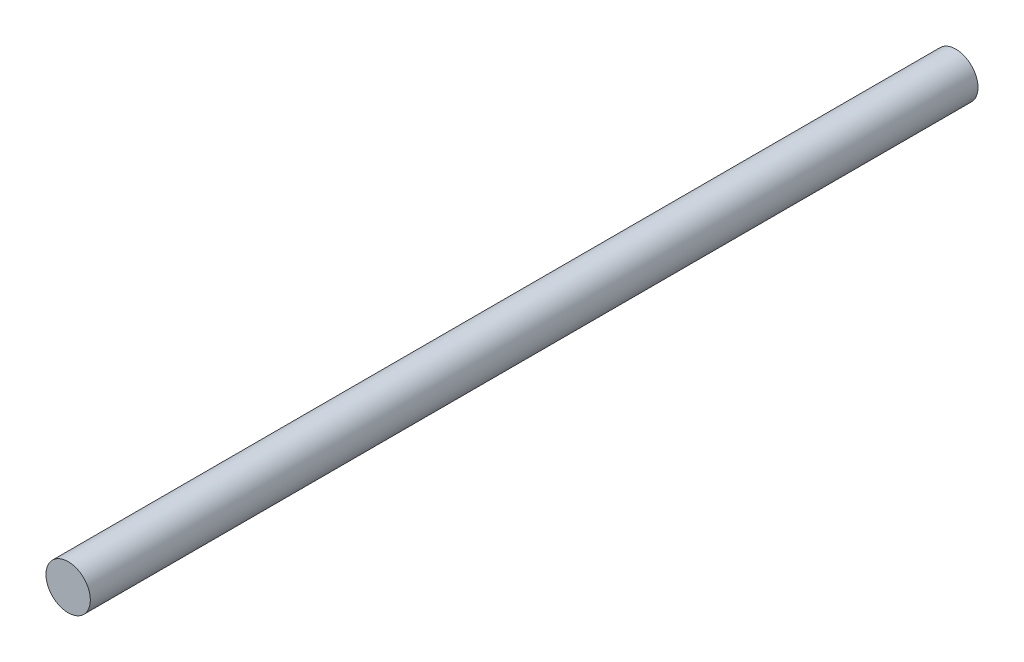
SolidWorks part; units mm, degrees
ref_plane "Front" through (0, 0, 0) normal (0, 0, 1) x (1, 0, 0)
ref_plane "Top" through (0, 0, 0) normal (0, 1, 0) x (1, 0, 0)
ref_plane "Right" through (0, 0, 0) normal (1, 0, 0) x (0, 0, -1)
sketch "Sketch1" plane through (0, 0, 0) normal (0, 0, 1) x (1, 0, 0)
  circle A0 centre (0, 0) radius 6.35
  dimension "D1" = 12.7
extrude "Boss-Extrude1" add sketch "Sketch1" along normal blind 254
